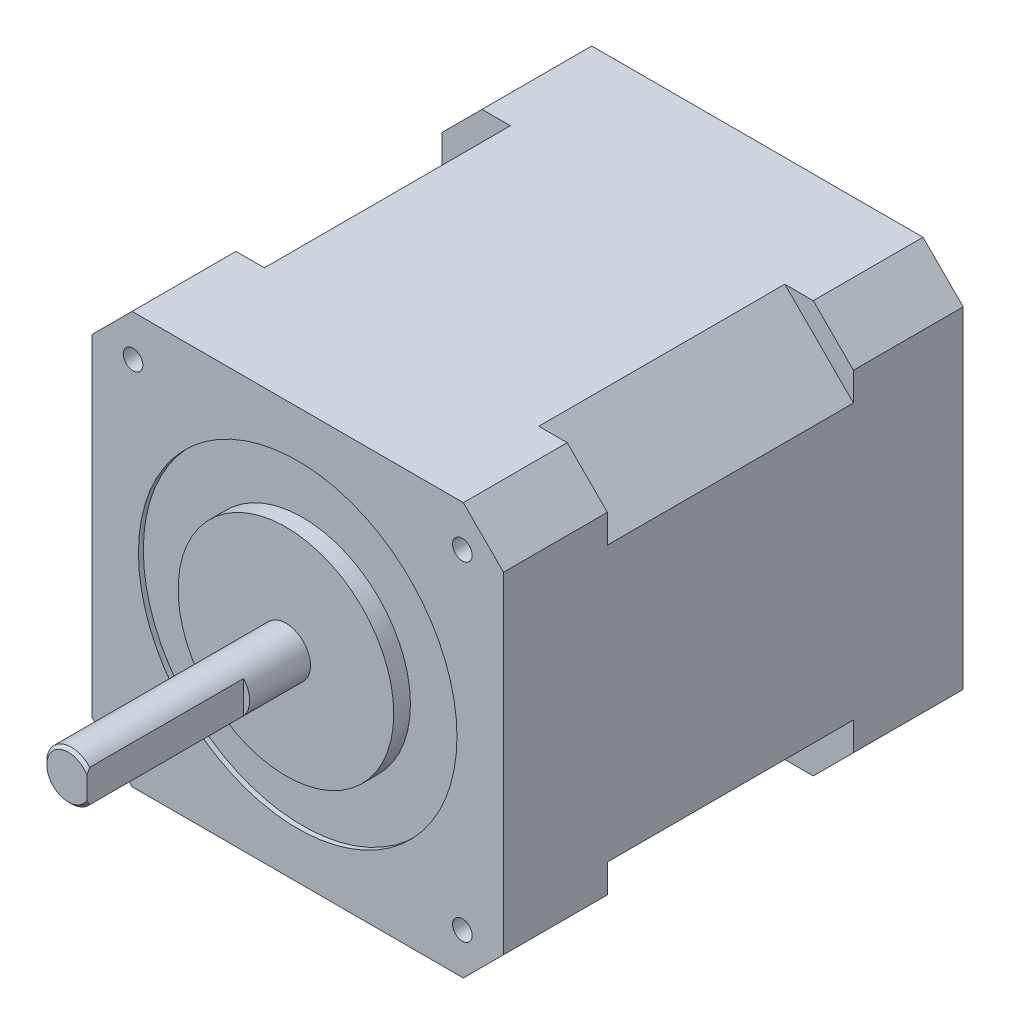
SolidWorks part; units mm, degrees
ref_plane "Plan de face" through (0, 0, 0) normal (0, 0, 1) x (1, 0, 0)
ref_plane "Plan de dessus" through (0, 0, 0) normal (0, 1, 0) x (1, 0, 0)
ref_plane "Plan de droite" through (0, 0, 0) normal (1, 0, 0) x (0, 0, -1)
sketch "Esquisse1" plane through (0, 0, 0) normal (0, 0, 1) x (1, 0, 0)
  line L0 (21, -16.9) -> (21, 16.9)
  line L1 (16.9, -21) -> (21, -16.9)
  line L2 (-16.9, 21) -> (-21, 16.9)
  line L3 (16.9, 21) -> (-16.9, 21)
  line L4 (16.9, 21) -> (21, 16.9)
  line L5 (16.9, -21) -> (-16.9, -21)
  line L6 (-16.9, -21) -> (-21, -16.9)
  line L7 (-21, -16.9) -> (-21, 16.9)
  line L8 (0, 26.608) -> (0, -33.2011) construction
  line L10 (44.1111, 0) -> (-50.7043, 0) construction
  point P2 (0, 21)
  point P4 (0, -21)
  point P10 (-21, 0)
  point P16 (21, 0)
  dimension "D1" = 21
  dimension "D2" = 16.9
  dimension "D3" = 21
  dimension "D4" = 16.9
extrude "Boss.-Extru.1" add sketch "Esquisse1" along normal blind 11.2
sketch "Esquisse2" plane through (0, 0, 11.2) normal (0, 0, 1) x (1, 0, 0)
  line L0 (14, 21) -> (21, 14)
  line L1 (16.9, 21) -> (-16.9, 21) construction
  line L2 (21, -16.9) -> (21, 16.9) construction
  line L3 (21, 14) -> (21, -14)
  line L4 (14, 21) -> (-14, 21)
  line L5 (-16.9227, 0) -> (0, 0) construction
  line L6 (0, 0) -> (0, 13.0635) construction
  line L7 (14, -21) -> (-14, -21)
  line L8 (14, -21) -> (21, -14)
  line L9 (-14, -21) -> (-21, -14)
  line L10 (-21, 14) -> (-21, -14)
  line L11 (-14, 21) -> (-21, 14)
  point P7 (-21, 0)
  point P15 (21, 0)
  point P18 (0, -21)
  point P19 (0, 21)
  dimension "D1" = 14
  dimension "D2" = 14
extrude "Boss.-Extru.2" add sketch "Esquisse2" along normal blind 25.1
sketch "Esquisse3" plane through (0, 0, 36.3) normal (0, 0, 1) x (1, 0, 0)
  line L0 (16.9, 21) -> (21, 16.9)
  line L1 (21, 16.9) -> (21, -16.9)
  line L2 (21, -14) -> (21, 14) construction
  line L3 (16.9, 21) -> (-16.9, 21)
  line L4 (14, 21) -> (-14, 21) construction
  line L5 (0, 8.2696) -> (0, -8.2696) construction
  line L6 (-8.1977, 0) -> (8.1977, 0) construction
  line L7 (16.9, -21) -> (-16.9, -21)
  line L8 (16.9, -21) -> (21, -16.9)
  line L9 (-16.9, -21) -> (-21, -16.9)
  line L10 (-21, 16.9) -> (-21, -16.9)
  line L11 (-16.9, 21) -> (-21, 16.9)
  point P18 (21, 0)
  point P19 (0, 0)
  point P21 (0, -21)
  point P22 (0, 21)
  point P23 (-21, 0)
extrude "Boss.-Extru.3" add sketch "Esquisse3" along normal blind 10.6
sketch "Esquisse4" plane through (0, 0, 46.9) normal (0, 0, 1) x (1, 0, 0)
  circle A0 centre (0, 0) radius 16.25
  dimension "D1" = 32.5
extrude "Enlèv. mat.-Extru.1" cut sketch "Esquisse4" against normal blind 0.5
sketch "Esquisse5" plane through (0, 0, 46.4) normal (0, 0, 1) x (1, 0, 0)
  circle A0 centre (0, 0) radius 11
  dimension "D1" = 22
extrude "Boss.-Extru.4" add sketch "Esquisse5" along normal blind 1.7
sketch "Esquisse6" plane through (0, 0, 48.1) normal (0, 0, 1) x (1, 0, 0)
  circle A0 centre (0, 0) radius 2.5
  dimension "D1" = 5
extrude "Boss.-Extru.5" add sketch "Esquisse6" along normal blind 22.2
chamfer "Chanfrein1" distance 0.3 angle 45 1 edges at (2.5, 0, 70.3)
sketch "Esquisse7" plane through (0, 0, 70.3) normal (0, 0, 1) x (1, 0, 0)
  line L0 (1.8782, 1.65) -> (1.8782, -1.65)
  circle A0 centre (0, 0) radius 2.5 construction
  circle A1 centre (0, 0) radius 2.5 construction
  arc A2 (1.8782, 1.65) -> (1.8782, -1.65) centre (0, 0) cw
  dimension "D1" = 3.3
extrude "Enlèv. mat.-Extru.2" cut sketch "Esquisse7" against normal blind 16
sketch "Esquisse8" plane through (0, 0, 46.9) normal (0, 0, 1) x (1, 0, 0)
  line L1 (-6.9992, 0) -> (0, 0) construction
  line L2 (0, 0) -> (0, 15.3647) construction
  line L4 (16.9, 21) -> (-16.9, 21) construction
  line L5 (-21, 16.9) -> (-21, -16.9) construction
  circle A0 centre (-16.8, 16.8) radius 1
  circle A1 centre (-16.8, -16.8) radius 1
  circle A2 centre (16.8, -16.8) radius 1
  circle A3 centre (16.8, 16.8) radius 1
  dimension "D1" = 2
  dimension "D2" = 4.2
  dimension "D3" = 4.2
extrude "Enlèv. mat.-Extru.3" cut sketch "Esquisse8" against normal blind 10
